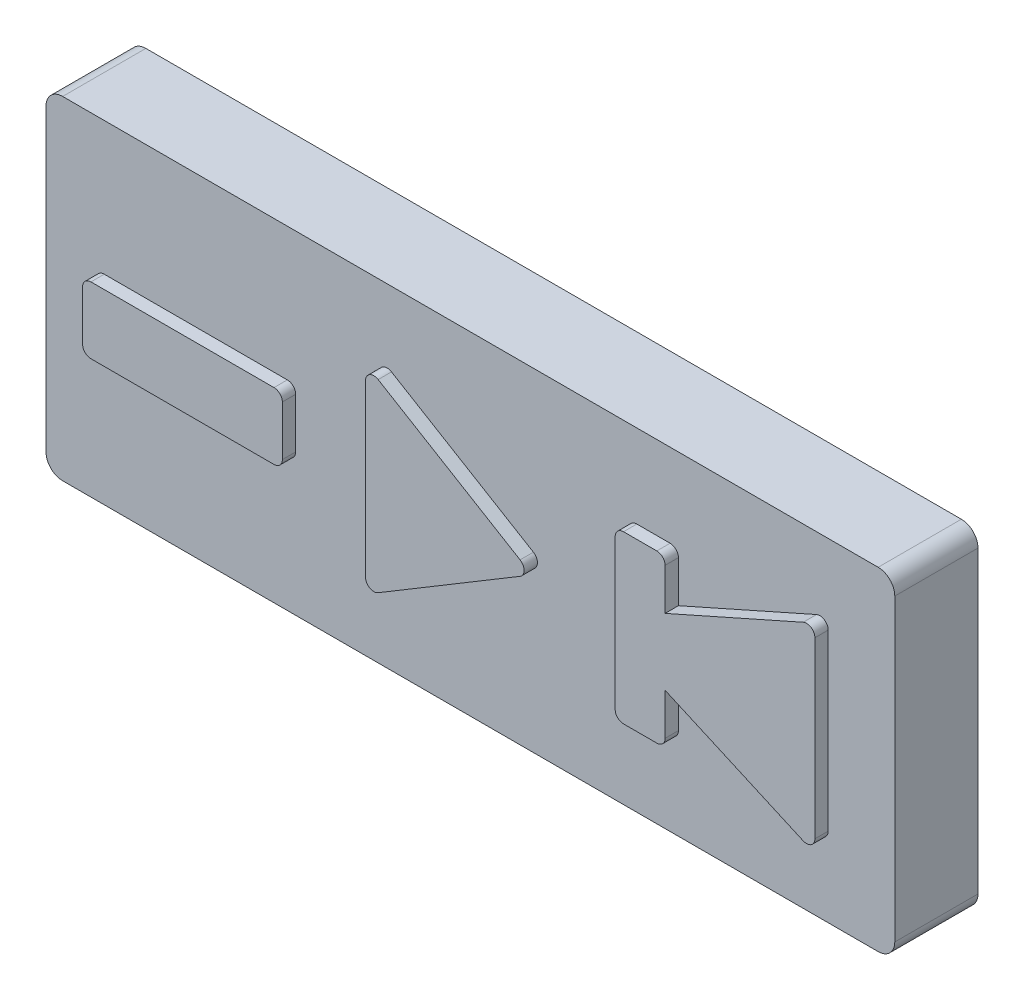
SolidWorks part; units mm, degrees
ref_plane "Front Plane" through (0, 0, 0) normal (0, 0, 1) x (1, 0, 0)
ref_plane "Top Plane" through (0, 0, 0) normal (0, 1, 0) x (1, 0, 0)
ref_plane "Right Plane" through (0, 0, 0) normal (1, 0, 0) x (0, 0, -1)
sketch "Sketch2" plane through (0, 0, 0) normal (0, 0, 1) x (1, 0, 0)
  line L0 (-5, 5.1169) -> (-5, -5.1169)
  line L1 (-4.2428, -5.5457) -> (4.2854, -0.4287)
  line L2 (4.2854, 0.4287) -> (-4.2428, 5.5457)
  line L3 (10, 4.5) -> (10, -4.5)
  line L4 (10.5, -5) -> (12.5, -5)
  line L5 (13, -4.5) -> (13, -2)
  line L6 (13, -2) -> (21.2969, -5.6875)
  line L7 (22, -5.2306) -> (22, 5.2306)
  line L8 (21.2969, 5.6875) -> (13, 2)
  line L9 (13, 2) -> (13, 4.5)
  line L10 (12.5, 5) -> (10.5, 5)
  line L12 (-21.5, 2) -> (-10.5, 2)
  line L13 (-22, 1.5) -> (-22, -1.5)
  line L14 (-21.5, -2) -> (-10.5, -2)
  line L15 (-10, 1.5) -> (-10, -1.5)
  arc A0 (21.2969, 5.6875) -> (22, 5.2306) centre (21.5, 5.2306) cw
  arc A1 (22, -5.2306) -> (21.2969, -5.6875) centre (21.5, -5.2306) cw
  arc A2 (12.5, -5) -> (13, -4.5) centre (12.5, -4.5) ccw
  arc A3 (10.5, -5) -> (10, -4.5) centre (10.5, -4.5) cw
  arc A4 (13, 4.5) -> (12.5, 5) centre (12.5, 4.5) ccw
  arc A5 (10, 4.5) -> (10.5, 5) centre (10.5, 4.5) cw
  arc A6 (4.2854, -0.4287) -> (4.2854, 0.4287) centre (4.0282, 0) ccw
  arc A7 (-4.2428, -5.5457) -> (-5, -5.1169) centre (-4.5, -5.1169) cw
  arc A8 (-4.2428, 5.5457) -> (-5, 5.1169) centre (-4.5, 5.1169) ccw
  arc A9 (-10.5, 2) -> (-10, 1.5) centre (-10.5, 1.5) cw
  arc A10 (-10.5, -2) -> (-10, -1.5) centre (-10.5, -1.5) ccw
  arc A11 (-22, -1.5) -> (-21.5, -2) centre (-21.5, -1.5) ccw
  arc A12 (-22, 1.5) -> (-21.5, 2) centre (-21.5, 1.5) cw
  dimension "D1" = 0.5
sketch "Sketch3" plane through (0, 0, 0) normal (0, 0, 1) x (1, 0, 0)
  line L1 (-24, 10) -> (25, 10)
  line L2 (-25, 9) -> (-25, -9)
  line L3 (-24, -10) -> (25, -10)
  line L4 (26, 9) -> (26, -9)
  arc A0 (25, 10) -> (26, 9) centre (25, 9) cw
  arc A1 (26, -9) -> (25, -10) centre (25, -9) cw
  arc A2 (-24, -10) -> (-25, -9) centre (-24, -9) cw
  arc A3 (-24, 10) -> (-25, 9) centre (-24, 9) ccw
  dimension "D1" = 1
ref_plane "Plane1" through (0, 0, 5) normal (0, 0, 1) x (1, 0, 0)
sketch "Sketch4" plane through (0, 0, 5) normal (0, 0, 1) x (1, 0, 0)
  line L0 (-5, 5.1169) -> (-5, -5.1169)
  line L1 (-4.2428, -5.5457) -> (4.2854, -0.4287)
  line L2 (4.2854, 0.4287) -> (-4.2428, 5.5457)
  line L3 (10, 4.5) -> (10, -4.5)
  line L4 (10.5, -5) -> (12.5, -5)
  line L5 (13, -4.5) -> (13, -2)
  line L6 (13, -2) -> (21.2969, -5.6875)
  line L7 (22, -5.2306) -> (22, 5.2306)
  line L8 (21.2969, 5.6875) -> (13, 2)
  line L9 (13, 2) -> (13, 4.5)
  line L10 (12.5, 5) -> (10.5, 5)
  line L12 (-21.5, 2) -> (-10.5, 2)
  line L13 (-22, 1.5) -> (-22, -1.5)
  line L14 (-21.5, -2) -> (-10.5, -2)
  line L15 (-10, 1.5) -> (-10, -1.5)
  arc A0 (21.2969, 5.6875) -> (22, 5.2306) centre (21.5, 5.2306) cw
  arc A1 (22, -5.2306) -> (21.2969, -5.6875) centre (21.5, -5.2306) cw
  arc A2 (12.5, -5) -> (13, -4.5) centre (12.5, -4.5) ccw
  arc A3 (10.5, -5) -> (10, -4.5) centre (10.5, -4.5) cw
  arc A4 (13, 4.5) -> (12.5, 5) centre (12.5, 4.5) ccw
  arc A5 (10, 4.5) -> (10.5, 5) centre (10.5, 4.5) cw
  arc A6 (4.2854, -0.4287) -> (4.2854, 0.4287) centre (4.0282, 0) ccw
  arc A7 (-4.2428, -5.5457) -> (-5, -5.1169) centre (-4.5, -5.1169) cw
  arc A8 (-4.2428, 5.5457) -> (-5, 5.1169) centre (-4.5, 5.1169) ccw
  arc A9 (-10.5, 2) -> (-10, 1.5) centre (-10.5, 1.5) cw
  arc A10 (-10.5, -2) -> (-10, -1.5) centre (-10.5, -1.5) ccw
  arc A11 (-22, -1.5) -> (-21.5, -2) centre (-21.5, -1.5) ccw
  arc A12 (-22, 1.5) -> (-21.5, 2) centre (-21.5, 1.5) cw
  dimension "D1" = 0.5
extrude "Boss-Extrude1" add sketch "Sketch3" along normal blind 5
sketch "Sketch5" plane through (0, 0, 5) normal (0, 0, 1) x (1, 0, 0)
  line L11 (-4.5, 5.1169) -> (-4.5, -5.1169)
  line L16 (-4.5, -5.1169) -> (4.0282, 0)
  line L17 (4.0282, 0) -> (-4.5, 5.1169)
  line L18 (10.5, 4.5) -> (10.5, -4.5)
  line L19 (10.5, -4.5) -> (12.5, -4.5)
  line L20 (12.5, -4.5) -> (12.5, -1.2306)
  line L21 (12.5, -1.2306) -> (21.5, -5.2306)
  line L22 (21.5, -5.2306) -> (21.5, 5.2306)
  line L23 (21.5, 5.2306) -> (12.5, 1.2306)
  line L24 (12.5, 1.2306) -> (12.5, 4.5)
  line L25 (12.5, 4.5) -> (10.5, 4.5)
  line L26 (-21.5, 1.5) -> (-10.5, 1.5)
  line L27 (-10.5, 1.5) -> (-10.5, -1.5)
  line L28 (-21.5, -1.5) -> (-10.5, -1.5)
  line L29 (-21.5, 1.5) -> (-21.5, -1.5)
sketch "Sketch6" plane through (0, 0, 0) normal (0, 0, 1) x (1, 0, 0)
  circle A0 centre (-16, 0) radius 0.75
  circle A1 centre (-1, 0) radius 0.75
  circle A2 centre (17, 0) radius 0.75
extrude "Cut-Extrude1" cut sketch "Sketch6" along normal blind 1
extrude "Boss-Extrude3" add sketch "Sketch4" along normal blind 0.8
